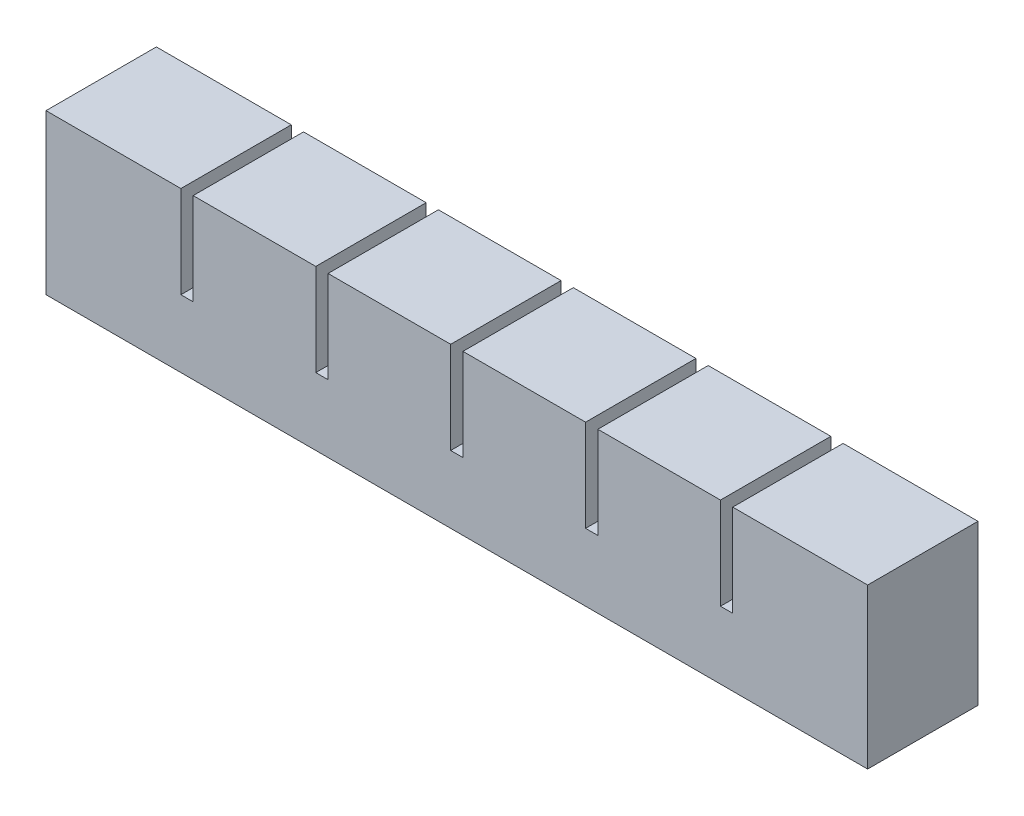
SolidWorks part; units mm, degrees
ref_plane "Front Plane" through (0, 0, 0) normal (0, 0, 1) x (1, 0, 0)
ref_plane "Top Plane" through (0, 0, 0) normal (0, 1, 0) x (1, 0, 0)
ref_plane "Right Plane" through (0, 0, 0) normal (1, 0, 0) x (0, 0, -1)
sketch "Sketch1" plane through (0, 0, 0) normal (0, 0, 1) x (1, 0, 0)
  line L1 (0, 0) -> (20, 0)
  line L2 (0, 0) -> (0, 20)
  line L3 (0, 20) -> (20, 20)
  line L4 (20, 0) -> (20, 20)
  dimension "D1" = 20
  dimension "D2" = 20
extrude "Boss-Extrude1" add sketch "Sketch1" along normal blind 18
sketch "Sketch2" plane through (0, 0, 0) normal (0, -1, 0) x (-1, 0, 0)
  line L0 (-20, -18) -> (-20, 0) construction
  line L1 (-6, -12) -> (-14, -12)
  line L2 (-6, -12) -> (-6, -6)
  line L3 (-6, -6) -> (-14, -6)
  line L4 (-14, -12) -> (-14, -6)
  line L5 (0, -18) -> (-20, -18) construction
  line L6 (0, -18) -> (0, 0) construction
  line L7 (0, 0) -> (-20, 0) construction
  dimension "D1" = 6
  dimension "D2" = 6
  dimension "D3" = 6
  dimension "D4" = 6
extrude "Cut-Extrude1" cut sketch "Sketch2" against normal blind 14
sketch "Sketch3" plane through (20, 0, 0) normal (1, 0, 0) x (0, 0, -1)
  line L0 (0, 0) -> (0, 20) construction
  line L1 (-18, 0) -> (0, 0)
  line L2 (-18, 0) -> (-18, 5)
  line L3 (-18, 5) -> (0, 5)
  line L4 (0, 0) -> (0, 5)
  dimension "D1" = 5
extrude "Boss-Extrude2" add sketch "Sketch3" along normal blind 2
pattern_linear "LPattern1" count 6 spacing 22 along (1, 0, 0) of bodies 103
sketch "Sketch4" plane through (130, 0, 0) normal (1, 0, 0) x (0, 0, -1)
  line L1 (-18, 5) -> (0, 5)
  line L2 (-18, 5) -> (-18, 20)
  line L3 (-18, 20) -> (0, 20)
  line L4 (0, 5) -> (0, 20)
extrude "Boss-Extrude3" add sketch "Sketch4" along normal up to surface (2 mm away) up to face at (132, 2.5, 9)
sketch "Sketch5" plane through (0, 0, 0) normal (-1, 0, 0) x (0, 0, 1)
  line L1 (0, 0) -> (18, 0)
  line L2 (0, 0) -> (0, 20)
  line L3 (0, 20) -> (18, 20)
  line L4 (18, 0) -> (18, 20)
extrude "Boss-Extrude4" add sketch "Sketch5" along normal blind 2
combine bodies "Combine1" operation type add bodies to combine 107 109 110 104 105 106
ref_point "Point1"
sketch "Sketch6" plane through (0, 0, 0) normal (0, -1, 0) x (-1, 0, 0)
  line L0 (-124, -6) -> (-124, -12) construction
  line L1 (-6, -8) -> (-124, -8)
  line L2 (-6, -8) -> (-6, -10)
  line L3 (-6, -10) -> (-124, -10)
  line L4 (-124, -8) -> (-124, -10)
  line L5 (-6, -8) -> (-124, -10) construction
  line L6 (-6, -10) -> (-124, -8) construction
  point P0 (-65, -9)
  dimension "D1" = 2
extrude "Cut-Extrude2" cut sketch "Sketch6" against normal blind 2
sketch "Sketch7" plane through (0, 0, 0) normal (0, -1, 0) x (-1, 0, 0)
  line L1 (2, -18) -> (-132, -18)
  line L2 (2, -18) -> (2, 0)
  line L3 (2, 0) -> (-132, 0)
  line L4 (-132, -18) -> (-132, 0)
extrude "Boss-Extrude5" add sketch "Sketch7" along normal blind 6
